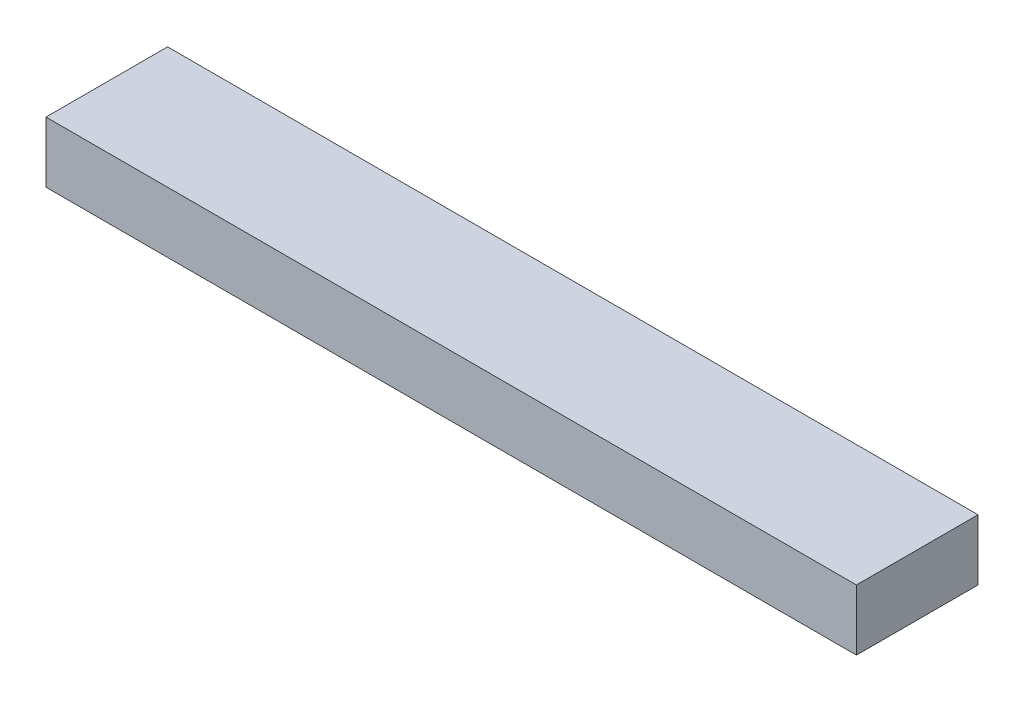
SolidWorks part; units mm, degrees
ref_plane "Front Plane" through (0, 0, 0) normal (0, 0, 1) x (1, 0, 0)
ref_plane "Top Plane" through (0, 0, 0) normal (0, 1, 0) x (1, 0, 0)
ref_plane "Right Plane" through (0, 0, 0) normal (1, 0, 0) x (0, 0, -1)
sketch "Sketch1" plane through (0, 0, 0) normal (0, 1, 0) x (1, 0, 0)
  line L1 (-1000, 150) -> (1000, 150)
  line L2 (-1000, 150) -> (-1000, -150)
  line L3 (-1000, -150) -> (1000, -150)
  line L4 (1000, 150) -> (1000, -150)
  line L5 (-1000, 150) -> (1000, -150) construction
  line L6 (-1000, -150) -> (1000, 150) construction
  point P0 (0, 0)
  dimension "D1" = 2000
  dimension "D2" = 300
extrude "Boss-Extrude1" add sketch "Sketch1" along normal mid plane 150
